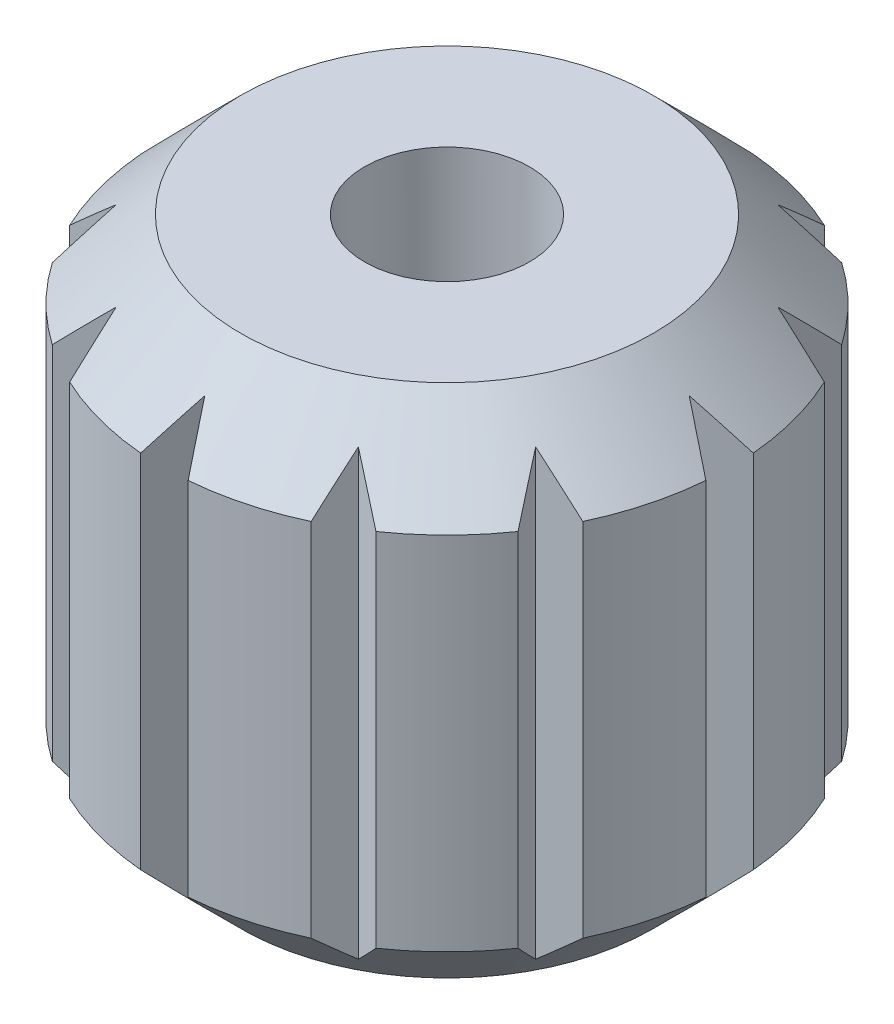
SolidWorks part; units mm, degrees
ref_plane "Front Plane" through (0, 0, 0) normal (0, 0, 1) x (1, 0, 0)
ref_plane "Top Plane" through (0, 0, 0) normal (0, 1, 0) x (1, 0, 0)
ref_plane "Right Plane" through (0, 0, 0) normal (1, 0, 0) x (0, 0, -1)
sketch "Sketch1" plane through (0, 0, 0) normal (0, 0, 1) x (1, 0, 0)
  line L0 (1.6, 0) -> (4, 0)
  line L1 (4, 0) -> (5.5, 1.5)
  line L2 (5.5, 1.5) -> (5.5, 8.5)
  line L3 (4, 10) -> (1.6, 10)
  line L4 (0, 9.5) -> (0, 0) construction
  line L7 (1.6, 10) -> (1.6, 0)
  line L8 (4, 10) -> (5.5, 8.5)
  point P5 (5.5, 1.5)
  dimension "D1" = 45
  dimension "D2" = 3.2
  dimension "D3" = 8
  dimension "D4" = 45
  dimension "D5" = 11
  dimension "D6" = 10
revolve "Revolve1" add sketch "Sketch1" angle 360 about L4
sketch "Sketch2" plane through (0, 10, 0) normal (0, 1, 0) x (1, 0, 0)
  line L0 (-0.85, 6.1451) -> (0, 4.6979)
  line L1 (0, 4.6979) -> (0.85, 6.1451)
  line L2 (0.85, 6.1451) -> (-0.85, 6.1451)
  line L3 (0, 0) -> (0, 8.8559) construction
  line L4 (3.8087, 4.8969) -> (2.3365, 5.7468)
  line L5 (2.3365, 5.7468) -> (2.3489, 4.0685)
  line L6 (2.3489, 4.0685) -> (3.8087, 4.8969)
  line L7 (5.7468, 2.3365) -> (4.8969, 3.8087)
  line L8 (4.8969, 3.8087) -> (4.0685, 2.3489)
  line L9 (4.0685, 2.3489) -> (5.7468, 2.3365)
  line L10 (6.1451, -0.85) -> (6.1451, 0.85)
  line L11 (6.1451, 0.85) -> (4.6979, 0)
  line L12 (4.6979, 0) -> (6.1451, -0.85)
  line L13 (4.8969, -3.8087) -> (5.7468, -2.3365)
  line L14 (5.7468, -2.3365) -> (4.0685, -2.3489)
  line L15 (4.0685, -2.3489) -> (4.8969, -3.8087)
  line L16 (2.3365, -5.7468) -> (3.8087, -4.8969)
  line L17 (3.8087, -4.8969) -> (2.3489, -4.0685)
  line L18 (2.3489, -4.0685) -> (2.3365, -5.7468)
  line L19 (-0.85, -6.1451) -> (0.85, -6.1451)
  line L20 (0.85, -6.1451) -> (0, -4.6979)
  line L21 (0, -4.6979) -> (-0.85, -6.1451)
  line L22 (-3.8087, -4.8969) -> (-2.3365, -5.7468)
  line L23 (-2.3365, -5.7468) -> (-2.3489, -4.0685)
  line L24 (-2.3489, -4.0685) -> (-3.8087, -4.8969)
  line L25 (-5.7468, -2.3365) -> (-4.8969, -3.8087)
  line L26 (-4.8969, -3.8087) -> (-4.0685, -2.3489)
  line L27 (-4.0685, -2.3489) -> (-5.7468, -2.3365)
  line L28 (-6.1451, 0.85) -> (-6.1451, -0.85)
  line L29 (-6.1451, -0.85) -> (-4.6979, 0)
  line L30 (-4.6979, 0) -> (-6.1451, 0.85)
  line L31 (-4.8969, 3.8087) -> (-5.7468, 2.3365)
  line L32 (-5.7468, 2.3365) -> (-4.0685, 2.3489)
  line L33 (-4.0685, 2.3489) -> (-4.8969, 3.8087)
  line L34 (-2.3365, 5.7468) -> (-3.8087, 4.8969)
  line L35 (-3.8087, 4.8969) -> (-2.3489, 4.0685)
  line L36 (-2.3489, 4.0685) -> (-2.3365, 5.7468)
  point P42 (0, 0)
  dimension "D1" = 12
extrude "Cut-Extrude1" cut sketch "Sketch2" against normal through all
ref_plane "Plane1" through (0, 3, 0) normal (0, -1, 0) x (-1, 0, 0)
sketch "Sketch3" plane through (0, 3, 0) normal (0, -1, 0) x (-1, 0, 0)
  line L1 (1.6743, 2.9) -> (-1.6743, 2.9)
  line L2 (-1.6743, 2.9) -> (-3.3486, 0)
  line L3 (-3.3486, 0) -> (-1.6743, -2.9)
  line L4 (-1.6743, -2.9) -> (1.6743, -2.9)
  line L5 (1.6743, -2.9) -> (3.3486, 0)
  line L6 (3.3486, 0) -> (1.6743, 2.9)
  circle A0 centre (0, 0) radius 2.9 construction
  dimension "D1" = 5.8
extrude "Cut-Extrude2" cut sketch "Sketch3" against normal blind 2.8
